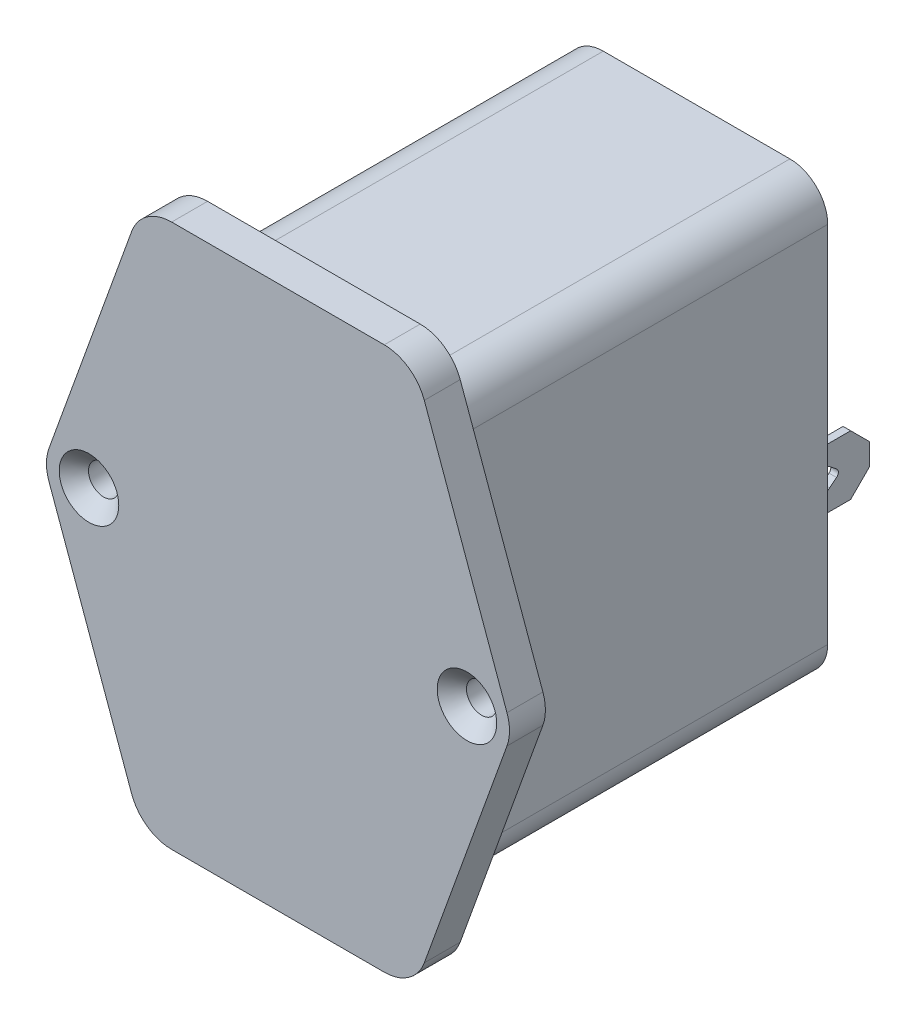
SolidWorks part; units mm, degrees
ref_plane "Front" through (0, 0, 0) normal (0, 0, 1) x (1, 0, 0)
ref_plane "Top" through (0, 0, 0) normal (0, 1, 0) x (1, 0, 0)
ref_plane "Right" through (0, 0, 0) normal (1, 0, 0) x (0, 0, -1)
sketch "Sketch1" plane through (0, 0, 0) normal (0, 0, 1) x (1, 0, 0)
  line L1 (0, 0) -> (27.75, 0)
  line L2 (0, 0) -> (0, 46.5)
  line L3 (0, 46.5) -> (27.75, 46.5)
  line L4 (27.75, 0) -> (27.75, 46.5)
  dimension "D1" = 27.75
  dimension "D2" = 46.5
extrude "Boss-Extrude1" add sketch "Sketch1" along normal blind 40.5
sketch "Sketch2" plane through (0, 0, 40.5) normal (0, 0, 1) x (1, 0, 0)
  line L0 (2.625, -5.2) -> (25.125, -5.2)
  line L1 (25.125, 52.3) -> (2.625, 52.3)
  line L2 (-1.6079, 49.3273) -> (-10.3579, 25.0773)
  line L3 (-10.3579, 22.0227) -> (-1.6079, -2.2273)
  line L4 (29.3579, -2.2273) -> (38.1079, 22.0227)
  line L5 (38.1079, 25.0773) -> (29.3579, 49.3273)
  line L6 (28.2853, 52.3) -> (28.2853, -5.2) construction
  line L7 (-0.5353, 52.3) -> (-0.5353, -5.2) construction
  line L8 (27.75, 46.5) -> (0, 46.5) construction
  line L9 (0, 46.5) -> (-0.5353, 46.5) construction
  line L10 (27.75, 46.5) -> (28.2853, 46.5) construction
  line L11 (38.659, 23.55) -> (28.2853, 23.55) construction
  line L12 (-0.5353, 23.55) -> (-10.909, 23.55) construction
  arc A0 (38.1079, 22.0227) -> (38.1079, 25.0773) centre (33.875, 23.55) ccw
  arc A1 (-10.3579, 25.0773) -> (-10.3579, 22.0227) centre (-6.125, 23.55) ccw
  circle A2 centre (-6.125, 23.55) radius 1.6
  circle A3 centre (33.875, 23.55) radius 1.6
  arc A4 (2.625, -5.2) -> (-1.6079, -2.2273) centre (2.625, -0.7) cw
  arc A5 (25.125, -5.2) -> (29.3579, -2.2273) centre (25.125, -0.7) ccw
  arc A6 (25.125, 52.3) -> (29.3579, 49.3273) centre (25.125, 47.8) cw
  arc A7 (2.625, 52.3) -> (-1.6079, 49.3273) centre (2.625, 47.8) ccw
  dimension "D3" = 4.5
  dimension "D4" = 3.2
  dimension "D5" = 40
  dimension "D6" = 4.5
  dimension "D1" = 57.5
  dimension "D2" = 5.8
  dimension "D7" = 22.5
extrude "Boss-Extrude2" add sketch "Sketch2" along normal blind 3.8
hole_wizard "CSK for M3 Flat Head Machine Screw1" positions "Sketch3" profile "Sketch4" countersink size "M3" standard "ANSI Metric" end condition through all
sketch "Sketch3" plane through (0, 0, 44.3) normal (0, 0, 1) x (1, 0, 0)
  point P0 (-6.125, 23.55)
  point P3 (33.875, 23.55)
sketch "Sketch4" plane through (-6.125, 23.55, 44.3) normal (1, 0, 0) x (0, -1, 0)
  line L0 (0, 0) -> (0, 44.3)
  line L1 (0, 44.3) -> (1.6, 44.3)
  line L2 (1.6, 44.3) -> (1.6, 1.55)
  line L3 (1.6, 1.55) -> (3.15, 0)
  line L5 (3.15, 0) -> (0, 0)
  line L6 (-1.6, 1.55) -> (-3.15, 0) construction
  line L11 (0, -6.35) -> (0, 107.95) construction
  dimension "Thru Hole Dia." = 3.2
  dimension "Thru Hole Depth" = 44.3
  dimension "Near C'Sink Dia." = 6.3
  dimension "Near C'Sink Angle" = 90
sketch "Sketch5" plane through (0, 0, 0) normal (0, 0, -1) x (-1, 0, 0)
  line L0 (-13.875, 0) -> (-13.875, 6.8546) construction
  line L1 (-22.975, 16.8) -> (-17.475, 16.8)
  line L2 (-22.975, 16.8) -> (-22.975, 7.5)
  line L3 (-22.975, 7.5) -> (-17.475, 7.5)
  line L4 (-17.475, 16.8) -> (-17.475, 7.5)
  line L5 (0, 0) -> (-27.75, 0) construction
  line L6 (-4.775, 7.5) -> (-10.275, 7.5)
  line L7 (-10.275, 16.8) -> (-10.275, 7.5)
  line L8 (-4.775, 16.8) -> (-10.275, 16.8)
  line L9 (-4.775, 16.8) -> (-4.775, 7.5)
  line L10 (0, 0) -> (-27.75, 0) construction
  dimension "D1" = 9.3
  dimension "D2" = 5.5
  dimension "D3" = 7.5
  dimension "D4" = 3.6
extrude "Boss-Extrude3" add sketch "Sketch5" along normal blind 2.5
ref_plane "Plane1" through (0, 5, 0) normal (0, -1, 0) x (-1, 0, 0)
sketch "Sketch6" plane through (0, 5, 0) normal (0, -1, 0) x (-1, 0, 0)
  line L0 (-13.875, 0) -> (-13.875, 11.5) construction
  line L1 (0, 0) -> (-27.75, 0) construction
  line L2 (-17.81, 0) -> (-17.81, 2.87)
  line L3 (-17.81, 2.87) -> (-17.025, 2.87)
  line L4 (-17.025, 2.87) -> (-17.025, 11.5)
  line L5 (-17.025, 11.5) -> (-10.725, 11.5)
  line L6 (-9.94, 0) -> (-9.94, 2.87)
  line L7 (-9.94, 2.87) -> (-10.725, 2.87)
  line L8 (-10.725, 2.87) -> (-10.725, 11.5)
  line L9 (-17.81, 0) -> (-9.94, 0)
  line L10 (-13.875, 8.5) -> (-14.8508, 7.2812)
  line L11 (-13.875, 8.5) -> (-12.8992, 7.2812)
  line L12 (-13.875, 6.5) -> (-13.875, 8.5) construction
  circle A0 centre (-13.875, 6.5) radius 1.25 construction
  arc A1 (-14.8508, 7.2812) -> (-12.8992, 7.2812) centre (-13.875, 6.5) ccw
  point P19 (-13.875, 8.5)
  dimension "D5" = 1.25
  dimension "D6" = 2
  dimension "D1" = 7.87
  dimension "D2" = 2.87
  dimension "D3" = 11.5
  dimension "D4" = 6.3
  dimension "D7" = 5
extrude "Boss-Extrude4" add sketch "Sketch6" along normal blind 0.8 separate body
chamfer "Chamfer1" distance 2 angle 45 2 edges at (17.025, 4.6, -11.5) (10.725, 4.6, -11.5)
fillet "Fillet1" radius 0.5 1 edges at (13.875, 4.6, -8.5)
ref_plane "Plane2" through (13.875, 0, 0) normal (1, 0, 0) x (0, 0, -1)
ref_plane "Plane3" through (19.875, 0, 0) normal (1, 0, 0) x (0, 0, -1)
sketch "Sketch7" plane through (19.875, 0, 0) normal (1, 0, 0) x (0, 0, -1)
  line L0 (2.5, 12.15) -> (11.5, 12.15) construction
  line L1 (2.5, 16.8) -> (2.5, 7.5) construction
  line L2 (11.5, 9) -> (11.5, 15.3)
  line L3 (11.5, 15.3) -> (2.5, 15.3)
  line L4 (11.5, 9) -> (2.5, 9)
  line L5 (2.5, 15.3) -> (2.5, 9)
  line L6 (11.5, 5) -> (11.5, 4.2) construction
  line L7 (7.2812, 13.1258) -> (8.5, 12.15)
  line L8 (8.5, 12.15) -> (7.2812, 11.1742)
  circle A0 centre (6.5, 12.15) radius 1.25 construction
  arc A1 (7.2812, 13.1258) -> (7.2812, 11.1742) centre (6.5, 12.15) ccw
  point P18 (8.5, 12.15)
  dimension "D2" = 2
  dimension "D3" = 1.25
  dimension "D1" = 6.3
  dimension "D4" = 5
extrude "Boss-Extrude5" add sketch "Sketch7" along normal blind 0.8 separate body
chamfer "Chamfer2" distance 2 angle 45 2 edges at (20.275, 15.3, -11.5) (20.275, 9, -11.5)
fillet "Fillet3" radius 0.5 1 edges at (20.275, 12.15, -8.5)
mirror "Mirror2" about plane through (13.875, 0, 0) normal (1, 0, 0) of bodies 106
fillet "Fillet2" radius 4 4 edges at (0, 46.5, 20.25) (0, 0, 20.25) (27.75, 46.5, 20.25) (27.75, 0, 20.25)
